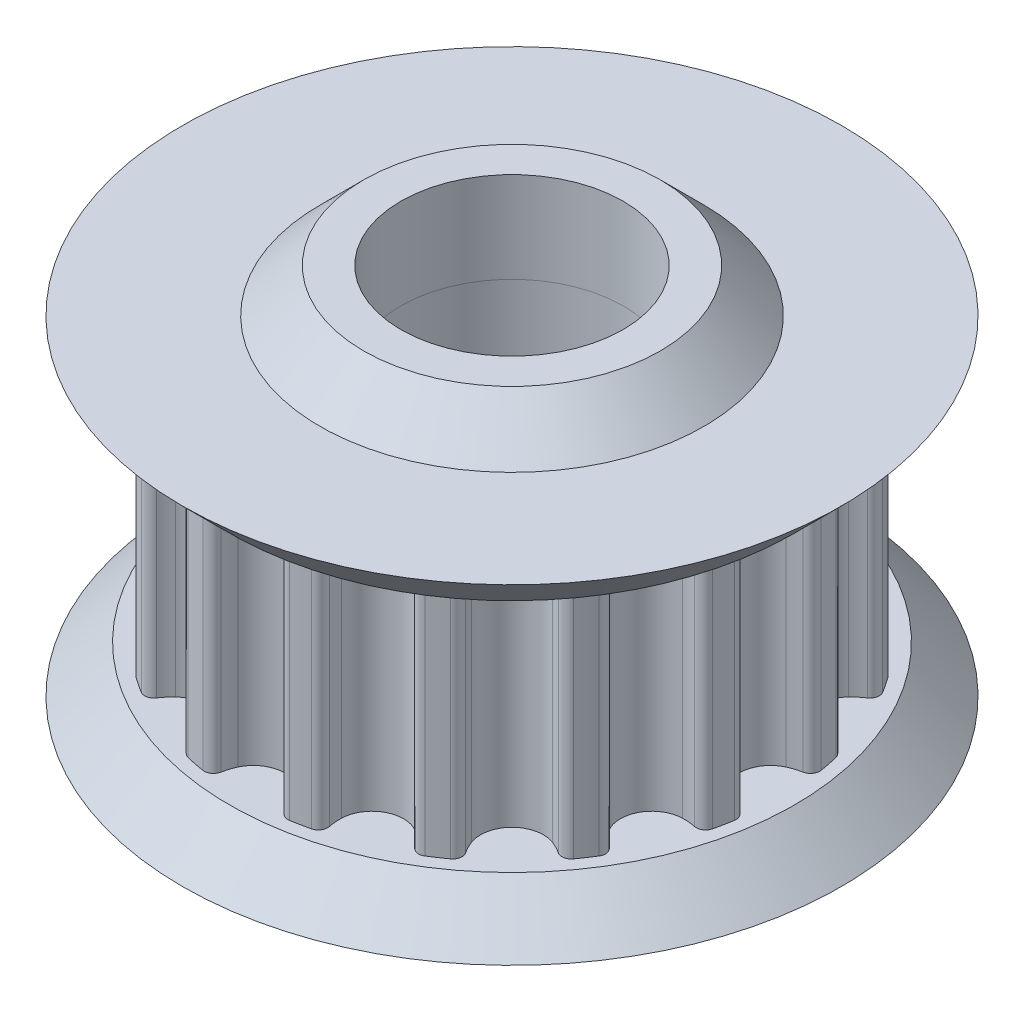
SolidWorks part; units mm, degrees
material "Alum Plate"
ref_plane "Front Plane" through (0, 0, 0) normal (0, 0, 1) x (1, 0, 0)
ref_plane "Top Plane" through (0, 0, 0) normal (0, 1, 0) x (1, 0, 0)
ref_plane "Right Plane" through (0, 0, 0) normal (1, 0, 0) x (0, 0, -1)
other "Bounding Box"
ref_plane "Default Plane" through (-8.9266, -12.7485, 0) normal (-0.1736, 0.9848, 0) x (0.9848, 0.1736, 0)
sketch "Sketch3" plane through (0, 0, 0) normal (0, 0, 1) x (1, 0, 0)
  line L0 (-7.62, 3.175) -> (-8.89, 4.445)
  line L1 (-7.62, 3.175) -> (7.62, 3.175)
  line L2 (-7.62, 3.175) -> (-7.62, -3.175)
  line L3 (-7.62, -3.175) -> (7.62, -3.175)
  line L4 (7.62, 3.175) -> (7.62, -3.175)
  line L5 (-7.62, 3.175) -> (7.62, -3.175) construction
  line L6 (-7.62, -3.175) -> (7.62, 3.175) construction
  line L7 (-8.89, 4.445) -> (-5.176, 4.445)
  line L8 (-5.176, 4.445) -> (-4, 5.621)
  line L9 (-4, 5.621) -> (0, 5.621)
  line L10 (0, 5.621) -> (0, 3.175)
  line L11 (0, -3.175) -> (0, -5.715)
  line L12 (0, -5.715) -> (-4, -5.715)
  line L13 (-4, -5.715) -> (-5.27, -4.445)
  line L14 (-5.27, -4.445) -> (-8.89, -4.445)
  line L15 (-8.89, -4.445) -> (-7.62, -3.175)
  line L16 (0, 11.4717) -> (0, 17.4749) construction
  line L17 (-3, -9.438) -> (-3, 11.1927) construction
  point P0 (0, 0)
  dimension "D1" = 6.35
  dimension "D2" = 15.24
  dimension "D3" = 45
  dimension "D4" = 45
  dimension "D5" = 11.336
  dimension "D6" = 45
  dimension "D7" = 8
  dimension "D8" = 2.54
  dimension "D9" = 1.27
  dimension "D10" = 1.27
  dimension "D11" = 3
sketch "Sketch1" plane through (0, 0, 0) normal (0, 1, 0) x (1, 0, 0)
  line L0 (0, -7.8245) -> (0, 0) construction
  circle A0 centre (0, 0) radius 3
  point P4 (-3, 0)
  point P5 (-6.1764, 3.8242)
  arc B0 (-1.8508, -6.777) -> (-1.6633, -7.0715) centre (-1.6061, -6.8282) ccw
  arc B1 (-1.6633, -7.0715) -> (-1.1695, -7.1697) centre (0, 0) ccw
  arc B2 (-1.1695, -7.1697) -> (-0.8836, -6.9694) centre (-1.1292, -6.923) ccw
  arc B3 (-0.7739, -6.6229) -> (-0.8836, -6.9694) centre (0.61, -7.2516) ccw
  arc B4 (0.7739, -6.6229) -> (-0.7739, -6.6229) centre (0, -6.9745) ccw
  arc B5 (0.8836, -6.9694) -> (0.7739, -6.6229) centre (-0.61, -7.2516) ccw
  arc B6 (0.8836, -6.9694) -> (1.1695, -7.1697) centre (1.1292, -6.923) ccw
  arc B7 (1.1695, -7.1697) -> (1.6633, -7.0715) centre (0, 0) ccw
  arc B8 (1.6633, -7.0715) -> (1.8508, -6.777) centre (1.6061, -6.8282) ccw
  arc B9 (1.8195, -6.4149) -> (1.8508, -6.777) centre (3.3386, -6.4662) ccw
  arc B10 (3.2495, -5.8226) -> (1.8195, -6.4149) centre (2.669, -6.4436) ccw
  arc B11 (3.4834, -6.1008) -> (3.2495, -5.8226) centre (2.2115, -6.9331) ccw
  arc B12 (3.4834, -6.1008) -> (3.8242, -6.1764) centre (3.6926, -5.9639) ccw
  arc B13 (3.8242, -6.1764) -> (4.2428, -5.8967) centre (0, 0) ccw
  arc B14 (4.2428, -5.8967) -> (4.3033, -5.5529) centre (4.0968, -5.6938) ccw
  arc B15 (4.1359, -5.2303) -> (4.3033, -5.5529) centre (5.559, -4.6963) ccw
  arc B16 (5.2303, -4.1359) -> (4.1359, -5.2303) centre (4.9317, -4.9317) ccw
  arc B17 (5.5529, -4.3033) -> (5.2303, -4.1359) centre (4.6963, -5.559) ccw
  arc B18 (5.5529, -4.3033) -> (5.8967, -4.2428) centre (5.6938, -4.0968) ccw
  arc B19 (5.8967, -4.2428) -> (6.1764, -3.8242) centre (0, 0) ccw
  arc B20 (6.1764, -3.8242) -> (6.1008, -3.4834) centre (5.9639, -3.6926) ccw
  arc B21 (5.8226, -3.2495) -> (6.1008, -3.4834) centre (6.9331, -2.2115) ccw
  arc B22 (6.4149, -1.8195) -> (5.8226, -3.2495) centre (6.4436, -2.669) ccw
  arc B23 (6.777, -1.8508) -> (6.4149, -1.8195) centre (6.4662, -3.3386) ccw
  arc B24 (6.777, -1.8508) -> (7.0715, -1.6633) centre (6.8282, -1.6061) ccw
  arc B25 (7.0715, -1.6633) -> (7.1697, -1.1695) centre (0, 0) ccw
  arc B26 (7.1697, -1.1695) -> (6.9694, -0.8836) centre (6.923, -1.1292) ccw
  arc B27 (6.6229, -0.7739) -> (6.9694, -0.8836) centre (7.2516, 0.61) ccw
  arc B28 (6.6229, 0.7739) -> (6.6229, -0.7739) centre (6.9745, 0) ccw
  arc B29 (6.9694, 0.8836) -> (6.6229, 0.7739) centre (7.2516, -0.61) ccw
  arc B30 (6.9694, 0.8836) -> (7.1697, 1.1695) centre (6.923, 1.1292) ccw
  arc B31 (7.1697, 1.1695) -> (7.0715, 1.6633) centre (0, 0) ccw
  arc B32 (7.0715, 1.6633) -> (6.777, 1.8508) centre (6.8282, 1.6061) ccw
  arc B33 (6.4149, 1.8195) -> (6.777, 1.8508) centre (6.4662, 3.3386) ccw
  arc B34 (5.8226, 3.2495) -> (6.4149, 1.8195) centre (6.4436, 2.669) ccw
  arc B35 (6.1008, 3.4834) -> (5.8226, 3.2495) centre (6.9331, 2.2115) ccw
  arc B36 (6.1008, 3.4834) -> (6.1764, 3.8242) centre (5.9639, 3.6926) ccw
  arc B37 (6.1764, 3.8242) -> (5.8967, 4.2428) centre (0, 0) ccw
  arc B38 (5.8967, 4.2428) -> (5.5529, 4.3033) centre (5.6938, 4.0968) ccw
  arc B39 (5.2303, 4.1359) -> (5.5529, 4.3033) centre (4.6963, 5.559) ccw
  arc B40 (4.1359, 5.2303) -> (5.2303, 4.1359) centre (4.9317, 4.9317) ccw
  arc B41 (4.3033, 5.5529) -> (4.1359, 5.2303) centre (5.559, 4.6963) ccw
  arc B42 (4.3033, 5.5529) -> (4.2428, 5.8967) centre (4.0968, 5.6938) ccw
  arc B43 (4.2428, 5.8967) -> (3.8242, 6.1764) centre (0, 0) ccw
  arc B44 (3.8242, 6.1764) -> (3.4834, 6.1008) centre (3.6926, 5.9639) ccw
  arc B45 (3.2495, 5.8226) -> (3.4834, 6.1008) centre (2.2115, 6.9331) ccw
  arc B46 (1.8195, 6.4149) -> (3.2495, 5.8226) centre (2.669, 6.4436) ccw
  arc B47 (1.8508, 6.777) -> (1.8195, 6.4149) centre (3.3386, 6.4662) ccw
  arc B48 (1.8508, 6.777) -> (1.6633, 7.0715) centre (1.6061, 6.8282) ccw
  arc B49 (1.6633, 7.0715) -> (1.1695, 7.1697) centre (0, 0) ccw
  arc B50 (1.1695, 7.1697) -> (0.8836, 6.9694) centre (1.1292, 6.923) ccw
  arc B51 (0.7739, 6.6229) -> (0.8836, 6.9694) centre (-0.61, 7.2516) ccw
  arc B52 (-0.7739, 6.6229) -> (0.7739, 6.6229) centre (0, 6.9745) ccw
  arc B53 (-0.8836, 6.9694) -> (-0.7739, 6.6229) centre (0.61, 7.2516) ccw
  arc B54 (-0.8836, 6.9694) -> (-1.1695, 7.1697) centre (-1.1292, 6.923) ccw
  arc B55 (-1.1695, 7.1697) -> (-1.6633, 7.0715) centre (0, 0) ccw
  arc B56 (-1.6633, 7.0715) -> (-1.8508, 6.777) centre (-1.6061, 6.8282) ccw
  arc B57 (-1.8195, 6.4149) -> (-1.8508, 6.777) centre (-3.3386, 6.4662) ccw
  arc B58 (-3.2495, 5.8226) -> (-1.8195, 6.4149) centre (-2.669, 6.4436) ccw
  arc B59 (-3.4834, 6.1008) -> (-3.2495, 5.8226) centre (-2.2115, 6.9331) ccw
  arc B60 (-3.4834, 6.1008) -> (-3.8242, 6.1764) centre (-3.6926, 5.9639) ccw
  arc B61 (-3.8242, 6.1764) -> (-4.2428, 5.8967) centre (0, 0) ccw
  arc B62 (-4.2428, 5.8967) -> (-4.3033, 5.5529) centre (-4.0968, 5.6938) ccw
  arc B63 (-4.1359, 5.2303) -> (-4.3033, 5.5529) centre (-5.559, 4.6963) ccw
  arc B64 (-5.2303, 4.1359) -> (-4.1359, 5.2303) centre (-4.9317, 4.9317) ccw
  arc B65 (-5.5529, 4.3033) -> (-5.2303, 4.1359) centre (-4.6963, 5.559) ccw
  arc B66 (-5.5529, 4.3033) -> (-5.8967, 4.2428) centre (-5.6938, 4.0968) ccw
  arc B67 (-5.8967, 4.2428) -> (-6.1764, 3.8242) centre (0, 0) ccw
  arc B68 (-6.1764, 3.8242) -> (-6.1008, 3.4834) centre (-5.9639, 3.6926) ccw
  arc B69 (-5.8226, 3.2495) -> (-6.1008, 3.4834) centre (-6.9331, 2.2115) ccw
  arc B70 (-6.4149, 1.8195) -> (-5.8226, 3.2495) centre (-6.4436, 2.669) ccw
  arc B71 (-6.777, 1.8508) -> (-6.4149, 1.8195) centre (-6.4662, 3.3386) ccw
  arc B72 (-6.777, 1.8508) -> (-7.0715, 1.6633) centre (-6.8282, 1.6061) ccw
  arc B73 (-7.0715, 1.6633) -> (-7.1697, 1.1695) centre (0, 0) ccw
  arc B74 (-7.1697, 1.1695) -> (-6.9694, 0.8836) centre (-6.923, 1.1292) ccw
  arc B75 (-6.6229, 0.7739) -> (-6.9694, 0.8836) centre (-7.2516, -0.61) ccw
  arc B76 (-6.6229, -0.7739) -> (-6.6229, 0.7739) centre (-6.9745, 0) ccw
  arc B77 (-6.9694, -0.8836) -> (-6.6229, -0.7739) centre (-7.2516, 0.61) ccw
  arc B78 (-6.9694, -0.8836) -> (-7.1697, -1.1695) centre (-6.923, -1.1292) ccw
  arc B79 (-7.1697, -1.1695) -> (-7.0715, -1.6633) centre (0, 0) ccw
  arc B80 (-7.0715, -1.6633) -> (-6.777, -1.8508) centre (-6.8282, -1.6061) ccw
  arc B81 (-6.4149, -1.8195) -> (-6.777, -1.8508) centre (-6.4662, -3.3386) ccw
  arc B82 (-5.8226, -3.2495) -> (-6.4149, -1.8195) centre (-6.4436, -2.669) ccw
  arc B83 (-6.1008, -3.4834) -> (-5.8226, -3.2495) centre (-6.9331, -2.2115) ccw
  arc B84 (-6.1008, -3.4834) -> (-6.1764, -3.8242) centre (-5.9639, -3.6926) ccw
  arc B85 (-6.1764, -3.8242) -> (-5.8967, -4.2428) centre (0, 0) ccw
  arc B86 (-5.8967, -4.2428) -> (-5.5529, -4.3033) centre (-5.6938, -4.0968) ccw
  arc B87 (-5.2303, -4.1359) -> (-5.5529, -4.3033) centre (-4.6963, -5.559) ccw
  arc B88 (-4.1359, -5.2303) -> (-5.2303, -4.1359) centre (-4.9317, -4.9317) ccw
  arc B89 (-4.3033, -5.5529) -> (-4.1359, -5.2303) centre (-5.559, -4.6963) ccw
  arc B90 (-4.3033, -5.5529) -> (-4.2428, -5.8967) centre (-4.0968, -5.6938) ccw
  arc B91 (-4.2428, -5.8967) -> (-3.8242, -6.1764) centre (0, 0) ccw
  arc B92 (-3.8242, -6.1764) -> (-3.4834, -6.1008) centre (-3.6926, -5.9639) ccw
  arc B93 (-3.2495, -5.8226) -> (-3.4834, -6.1008) centre (-2.2115, -6.9331) ccw
  arc B94 (-1.8195, -6.4149) -> (-3.2495, -5.8226) centre (-2.669, -6.4436) ccw
  arc B95 (-1.8508, -6.777) -> (-1.8195, -6.4149) centre (-3.3386, -6.4662) ccw
sketch_block_instance "Block-GT2 16 Tooth Profile-1"
sketch_block "Block-GT2 16 Tooth Profile"
extrude "Boss-Extrude1" add sketch "Sketch1" along normal mid plane 6.35
sketch "Sketch4" plane through (0, 0, 0) normal (0, 0, 1) x (1, 0, 0)
  line L0 (-7.62, 3.175) -> (-3, 3.175)
  line L1 (-7.62, 3.175) -> (7.62, 3.175) construction
  line L2 (-3, 3.175) -> (-3, 5.621)
  line L3 (-4, 5.621) -> (0, 5.621) construction
  line L4 (-3, 5.621) -> (-4, 5.621)
  line L5 (-4, 5.621) -> (-5.176, 4.445)
  line L6 (-5.176, 4.445) -> (-8.89, 4.445)
  line L7 (-8.89, 4.445) -> (-7.62, 3.175)
  line L8 (-7.62, -3.175) -> (-8.89, -4.445)
  line L9 (-8.89, -4.445) -> (-5.27, -4.445)
  line L10 (-5.27, -4.445) -> (-4, -5.715)
  line L11 (-4, -5.715) -> (-3, -5.715)
  line L12 (0, -5.715) -> (-4, -5.715) construction
  line L13 (-3, -5.715) -> (-3, -3.175)
  line L14 (-7.62, -3.175) -> (7.62, -3.175) construction
  line L15 (-3, -3.175) -> (-7.62, -3.175)
  line L17 (0, 0) -> (0, 6.3277) construction
  line L21 (-3, -200009.438) -> (-3, 200011.1927) construction
revolve "Revolve1" add sketch "Sketch4" angle 360 about L17
